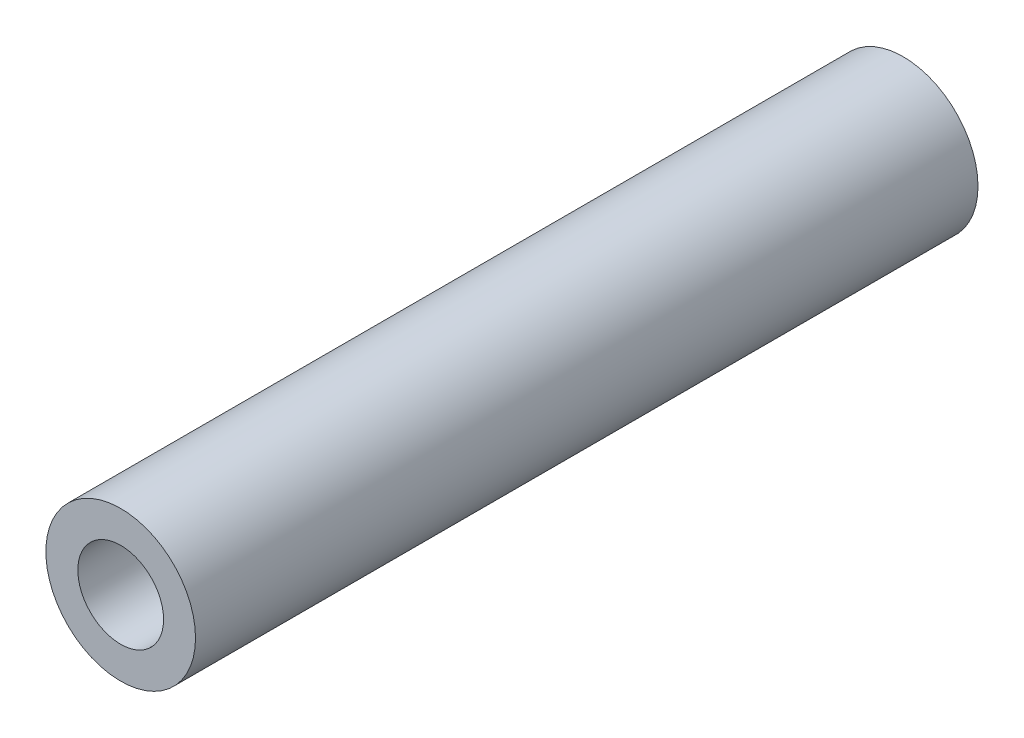
SolidWorks part; units mm, degrees
ref_plane "Front Plane" through (0, 0, 0) normal (0, 0, 1) x (1, 0, 0)
ref_plane "Top Plane" through (0, 0, 0) normal (0, 1, 0) x (1, 0, 0)
ref_plane "Right Plane" through (0, 0, 0) normal (1, 0, 0) x (0, 0, -1)
sketch "Sketch1" plane through (0, 0, 0) normal (0, 0, 1) x (1, 0, 0)
  circle A0 centre (0, 0) radius 2.4384
  circle A1 centre (0, 0) radius 1.397
  dimension "D1" = 4.8768
  dimension "D2" = 2.794
extrude "Boss-Extrude1" add sketch "Sketch1" along normal blind 25.4991
